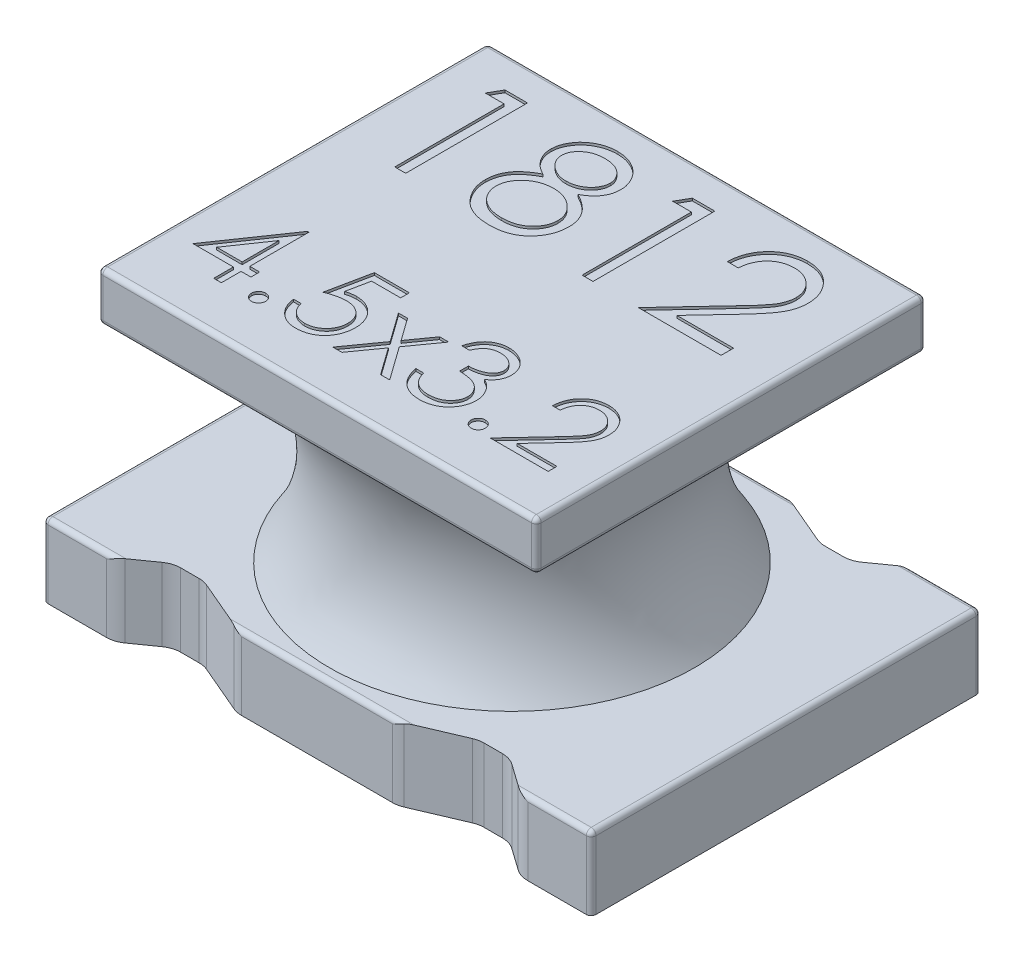
SolidWorks part; units mm, degrees
ref_plane "Front Plane" through (0, 0, 0) normal (0, 0, 1) x (1, 0, 0)
ref_plane "Top Plane" through (0, 0, 0) normal (0, 1, 0) x (1, 0, 0)
ref_plane "Right Plane" through (0, 0, 0) normal (1, 0, 0) x (0, 0, -1)
sketch "Sketch1" plane through (0, 0, 0) normal (0, 1, 0) x (1, 0, 0)
  line L0 (2.25, -1.6) -> (-2.25, 1.6) construction
  line L1 (-2.25, 1.6) -> (2.25, 1.6)
  line L2 (-2.25, 1.6) -> (-2.25, -1.6)
  line L3 (-2.25, -1.6) -> (2.25, -1.6)
  line L4 (2.25, 1.6) -> (2.25, -1.6)
  dimension "D1" = 4.5
  dimension "D2" = 3.2
extrude "Boss-Extrude1" add sketch "Sketch1" along normal blind 2.6
sketch "Sketch3" plane through (0, 0, 0) normal (1, 0, 0) x (0, 0, -1)
  line L0 (0, 0) -> (0, 2.9759) construction
  line L1 (3.2, 2.2) -> (3.2, 0.6)
  line L2 (3.2, 0.6) -> (1.5, 0.6)
  line L3 (3.2, 2.2) -> (1.5, 2.2)
  line L4 (-1.6, 2.6) -> (1.6, 2.6) construction
  line L5 (-1.6, 0) -> (1.6, 0) construction
  arc A0 (1.5, 2.2) -> (1.5, 0.6) centre (2.6489, 1.4) ccw
  dimension "D5" = 1.4
  dimension "D1" = 3.2
  dimension "D2" = 0.4
  dimension "D3" = 0.6
  dimension "D4" = 1.5
revolve "Cut-Revolve1" cut sketch "Sketch3" angle 360 about L0
sketch "Sketch4" plane through (0, 2.6, 0) normal (0, 1, 0) x (1, 0, 0)
  line L0 (0, 0) -> (0, 2.2993) construction
  line L1 (1.8, 1.75) -> (2.8, 1.75)
  line L2 (1.8, 1.75) -> (1.8, -1.75)
  line L3 (1.8, -1.75) -> (2.8, -1.75)
  line L4 (2.8, 1.75) -> (2.8, -1.75)
  line L5 (-1.8, 1.75) -> (-2.8, 1.75)
  line L6 (-1.8, 1.75) -> (-1.8, -1.75)
  line L7 (-1.8, -1.75) -> (-2.8, -1.75)
  line L8 (-2.8, 1.75) -> (-2.8, -1.75)
  line L9 (0, 0) -> (1.8, 0) construction
  dimension "D1" = 3.6
  dimension "D2" = 1
  dimension "D3" = 3.5
extrude "Cut-Extrude2" cut sketch "Sketch4" against normal blind 1.5
fillet "Fillet1" radius 0.04 20 edges at (0, 0.6, -1.6) (0, 0.6, 1.6) (0, 2.2, -1.6) (1.8, 2.4, -1.6) (1.8, 2.2, 0) (-1.8, 2.2, 0) (-1.8, 2.4, -1.6) (1.8, 2.4, 1.6) (0, 2.2, 1.6) (-1.8, 2.4, 1.6) (0, 2.6, -1.6) (1.8, 2.6, 0) (0, 2.6, 1.6) (-1.8, 2.6, 0) (-2.25, 0.3, -1.6) (-2.25, 0.6, 0) (-2.25, 0.3, 1.6) (2.25, 0.6, 0) (2.25, 0.3, -1.6) (2.25, 0.3, 1.6)
sketch "Sketch5" plane through (0, 0, 0) normal (0, -1, 0) x (1, 0, 0)
  line L0 (-1.6145, 1.5633) -> (-1.4355, 1.4367)
  line L1 (-2.21, 1.6) -> (2.21, 1.6) construction
  line L2 (-1.32, 1.4) -> (-1.17, 1.4)
  line L3 (-1.0914, 1.4161) -> (-0.6986, 1.5839)
  line L4 (-1.73, 1.6) -> (-1.85, 1.6)
  line L5 (-1.85, 1.6) -> (-1.85, 1.9)
  line L6 (-1.85, 1.9) -> (-0.5, 1.9)
  line L7 (-0.5, 1.9) -> (-0.5, 1.6)
  line L8 (-0.5, 1.6) -> (-0.62, 1.6)
  line L9 (-2.25, -1.56) -> (-2.25, 1.56) construction
  line L10 (0, 0) -> (-0.7358, 0) construction
  line L11 (0, 0) -> (0, -0.3494) construction
  line L12 (-0.5, -1.6) -> (-0.62, -1.6)
  line L13 (-0.5, -1.9) -> (-0.5, -1.6)
  line L14 (-1.85, -1.9) -> (-0.5, -1.9)
  line L15 (-1.85, -1.6) -> (-1.85, -1.9)
  line L16 (-1.73, -1.6) -> (-1.85, -1.6)
  line L17 (-1.0914, -1.4161) -> (-0.6986, -1.5839)
  line L18 (-1.32, -1.4) -> (-1.17, -1.4)
  line L19 (-1.6145, -1.5633) -> (-1.4355, -1.4367)
  line L20 (1.6145, -1.5633) -> (1.4355, -1.4367)
  line L21 (1.32, -1.4) -> (1.17, -1.4)
  line L22 (1.0914, -1.4161) -> (0.6986, -1.5839)
  line L23 (1.73, -1.6) -> (1.85, -1.6)
  line L24 (1.85, -1.6) -> (1.85, -1.9)
  line L25 (1.85, -1.9) -> (0.5, -1.9)
  line L26 (0.5, -1.9) -> (0.5, -1.6)
  line L27 (0.5, -1.6) -> (0.62, -1.6)
  line L28 (0.5, 1.6) -> (0.62, 1.6)
  line L29 (0.5, 1.9) -> (0.5, 1.6)
  line L30 (1.85, 1.9) -> (0.5, 1.9)
  line L31 (1.85, 1.6) -> (1.85, 1.9)
  line L32 (1.73, 1.6) -> (1.85, 1.6)
  line L33 (1.0914, 1.4161) -> (0.6986, 1.5839)
  line L34 (1.32, 1.4) -> (1.17, 1.4)
  line L35 (1.6145, 1.5633) -> (1.4355, 1.4367)
  arc A0 (-0.62, 1.6) -> (-0.6986, 1.5839) centre (-0.62, 1.4) ccw
  arc A1 (-1.0914, 1.4161) -> (-1.17, 1.4) centre (-1.17, 1.6) cw
  arc A2 (-1.32, 1.4) -> (-1.4355, 1.4367) centre (-1.32, 1.6) cw
  arc A3 (-1.73, 1.6) -> (-1.6145, 1.5633) centre (-1.73, 1.4) cw
  arc A4 (-1.73, -1.6) -> (-1.6145, -1.5633) centre (-1.73, -1.4) ccw
  arc A5 (-1.32, -1.4) -> (-1.4355, -1.4367) centre (-1.32, -1.6) ccw
  arc A6 (-1.0914, -1.4161) -> (-1.17, -1.4) centre (-1.17, -1.6) ccw
  arc A7 (-0.62, -1.6) -> (-0.6986, -1.5839) centre (-0.62, -1.4) cw
  arc A8 (0.62, -1.6) -> (0.6986, -1.5839) centre (0.62, -1.4) ccw
  arc A9 (1.0914, -1.4161) -> (1.17, -1.4) centre (1.17, -1.6) cw
  arc A10 (1.32, -1.4) -> (1.4355, -1.4367) centre (1.32, -1.6) cw
  arc A11 (1.73, -1.6) -> (1.6145, -1.5633) centre (1.73, -1.4) cw
  arc A12 (1.73, 1.6) -> (1.6145, 1.5633) centre (1.73, 1.4) ccw
  arc A13 (1.32, 1.4) -> (1.4355, 1.4367) centre (1.32, 1.6) ccw
  arc A14 (1.0914, 1.4161) -> (1.17, 1.4) centre (1.17, 1.6) ccw
  arc A15 (0.62, 1.6) -> (0.6986, 1.5839) centre (0.62, 1.4) cw
  point P12 (-0.6609, 1.6)
  point P19 (-1.6664, 1.6)
  point P42 (-1.6664, -1.6)
  point P43 (-0.6609, -1.6)
  point P76 (0.6609, -1.6)
  point P77 (1.6664, -1.6)
  point P78 (1.6664, 1.6)
  point P79 (0.6609, 1.6)
  dimension "D1" = 0.2
  dimension "D2" = 0.4
  dimension "D3" = 0.5
  dimension "D4" = 0.15
  dimension "D5" = 0.12
  dimension "D6" = 0.12
  dimension "D7" = 0.2
  dimension "D8" = 1.17
  dimension "D9" = 0.3
extrude "Cut-Extrude3" cut sketch "Sketch5" against normal blind 1
sketch "Sketch6" plane through (0, 2.6, 0) normal (0, 1, 0) x (1, 0, 0)
  text T0 "1812" font "Century Gothic" height 1
extrude "Cut-Extrude4" cut sketch "Sketch6" against normal blind 0.02
sketch "Sketch7" plane through (0, 2.6, 0) normal (0, 1, 0) x (1, 0, 0)
  text T0 "4.5x3.2" font "Century Gothic" height 0.7
extrude "Cut-Extrude5" cut sketch "Sketch7" against normal blind 0.02
